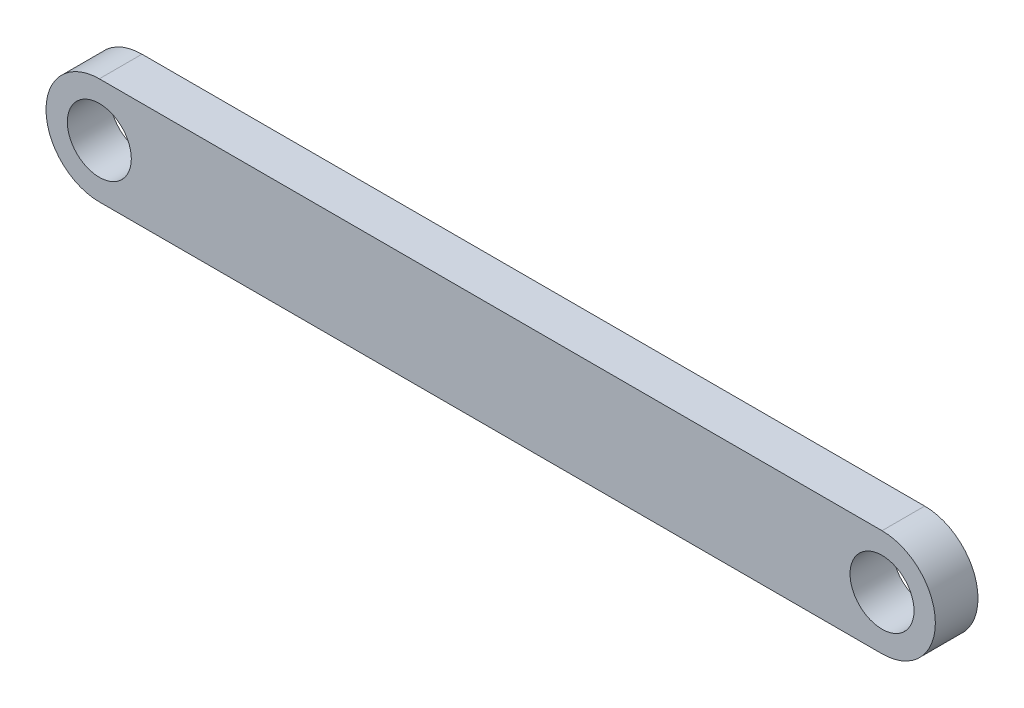
SolidWorks part; units mm, degrees
ref_plane "Front Plane" through (0, 0, 0) normal (0, 0, 1) x (1, 0, 0)
ref_plane "Top Plane" through (0, 0, 0) normal (0, 1, 0) x (1, 0, 0)
ref_plane "Right Plane" through (0, 0, 0) normal (1, 0, 0) x (0, 0, -1)
sketch "Sketch1" plane through (0, 0, 0) normal (0, 0, 1) x (1, 0, 0)
  line L0 (0.1487, 0.0295) -> (36.8487, 0.0295) construction
  line L1 (0.1487, 2.5295) -> (36.8487, 2.5295)
  line L2 (0.1487, -2.4705) -> (36.8487, -2.4705)
  arc A0 (0.1487, 2.5295) -> (0.1487, -2.4705) centre (0.1487, 0.0295) ccw
  arc A1 (36.8487, -2.4705) -> (36.8487, 2.5295) centre (36.8487, 0.0295) ccw
  circle A2 centre (0.1487, 0.0295) radius 1.5
  circle A3 centre (36.8487, 0.0295) radius 1.5
  point P2 (18.4987, 0.0295)
  dimension "D3" = 3
  dimension "D4" = 3
  dimension "D1" = 36.7
  dimension "D2" = 5
extrude "Boss-Extrude1" add sketch "Sketch1" along normal blind 2 contours L2 A1 L1 A0 | A2 | A3
